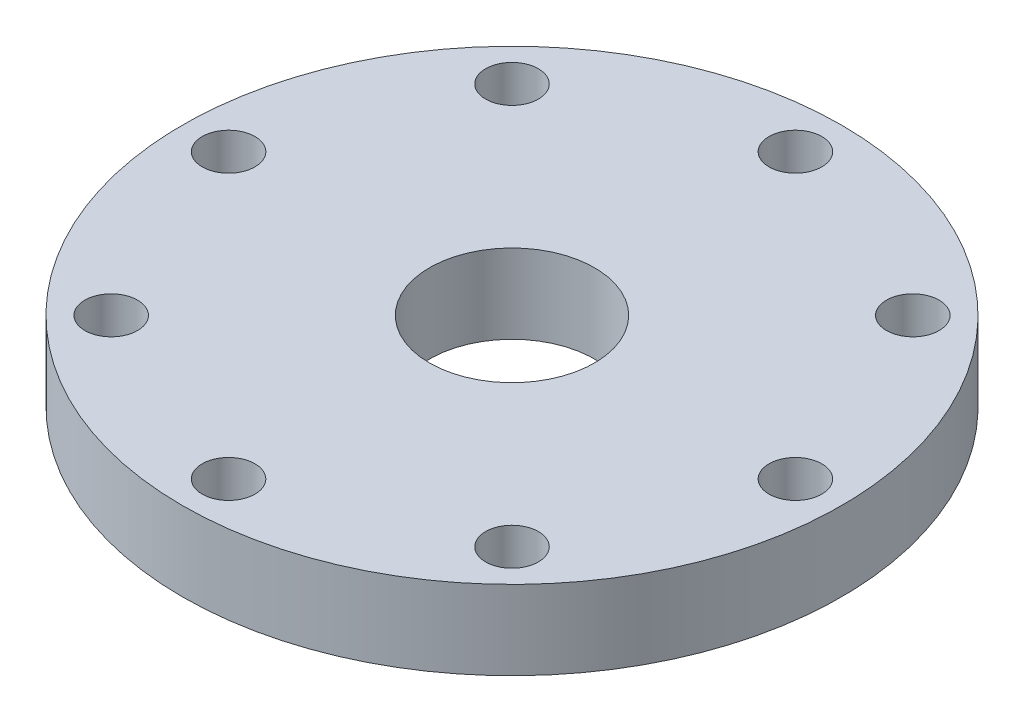
SolidWorks part; units mm, degrees
ref_plane "前视基准面" through (0, 0, 0) normal (0, 0, 1) x (1, 0, 0)
ref_plane "上视基准面" through (0, 0, 0) normal (0, 1, 0) x (1, 0, 0)
ref_plane "右视基准面" through (0, 0, 0) normal (1, 0, 0) x (0, 0, -1)
other "Configuration Table"
sketch "草图1" plane through (0, 0, 0) normal (0, 1, 0) x (1, 0, 0)
  circle A0 centre (0, 0) radius 25
  circle A1 centre (0, 0) radius 21.5 construction
  circle A2 centre (0, 21.5) radius 2
  circle A3 centre (15.2028, 15.2028) radius 2
  circle A4 centre (21.5, 0) radius 2
  circle A5 centre (15.2028, -15.2028) radius 2
  circle A6 centre (0, -21.5) radius 2
  circle A7 centre (-15.2028, -15.2028) radius 2
  circle A8 centre (-21.5, 0) radius 2
  circle A9 centre (-15.2028, 15.2028) radius 2
  circle A10 centre (0, 0) radius 6.2607
  point P6 (0, 0)
  point P23 (0, 0)
  dimension "D1" = 50
  dimension "D3" = 4
  dimension "D6" = 21.5
  dimension "D7" = 12.5213
  dimension "D4" = 8
extrude "凸台-拉伸1" add sketch "草图1" along normal blind 6 contours A2 | A3 | A4 | A5 | A10 | A0 | A6 | A7 | A8 | A9
